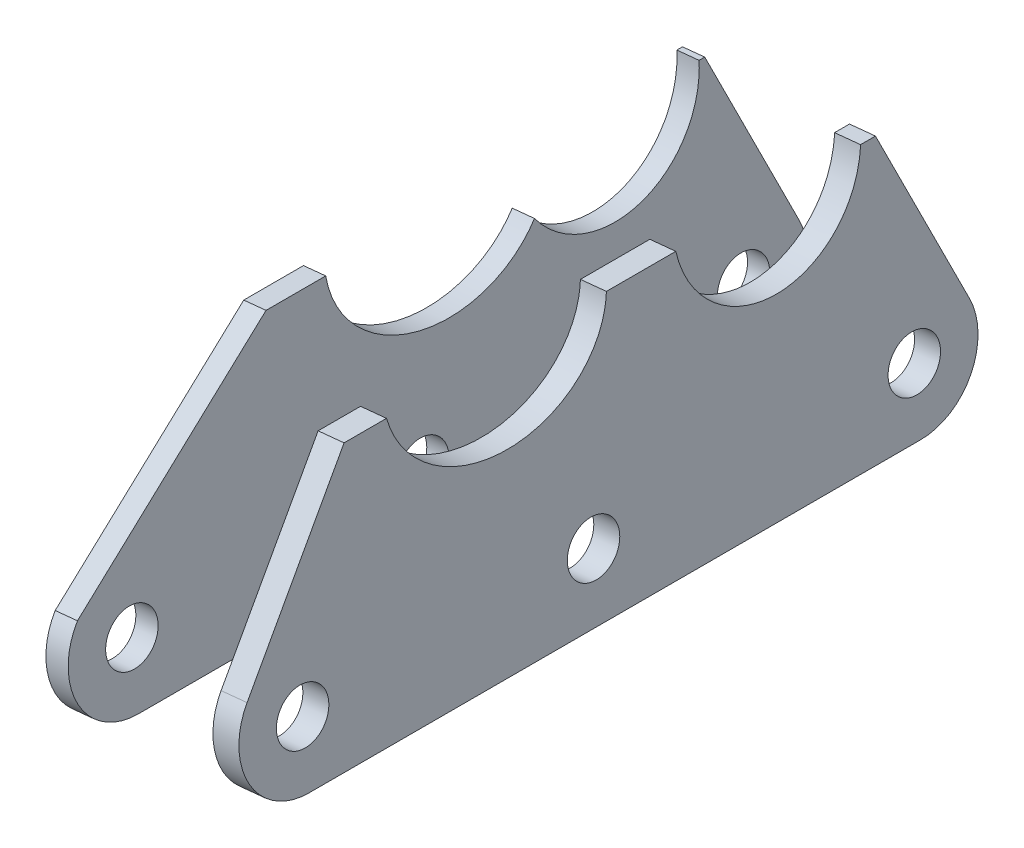
SolidWorks part; units mm, degrees
material "1.0545 (S355N)"
ref_plane "Płaszczyzna XY" through (0, 0, 0) normal (0, 0, 1) x (1, 0, 0)
ref_plane "Płaszczyzna XZ" through (0, 0, 0) normal (0, 1, 0) x (1, 0, 0)
ref_plane "Płaszczyzna YZ" through (0, 0, 0) normal (1, 0, 0) x (0, 0, -1)
ref_plane "Płaszczyzna1" through (1510.2654, 150.1623, 0) normal (-0.9951, -0.0989, 0) x (0, 0, 1)
ref_plane "Płaszczyzna2" through (1487.3783, 147.8867, 0) normal (-0.9951, -0.0989, 0) x (0, 0, 1)
sketch "Szkic1" plane through (1510.2654, 150.1623, 0) normal (-0.9951, -0.0989, 0) x (0, 0, 1)
  line L0 (176, -389.2443) -> (94, -389.2443)
  line L1 (162.1321, -354.2443) -> (167.8211, -354.2443)
  line L2 (96.5848, -354.2443) -> (86.2462, -377.2616)
  line L3 (132.653, -354.2443) -> (123.3511, -354.2443)
  line L4 (96.5848, -354.2443) -> (98.5848, -354.2443)
  line L6 (123.3511, -354.2443) -> (132.653, -354.2443)
  line L7 (167.8211, -354.2443) -> (182.9628, -375.8689)
  circle A0 centre (176, -380.7443) radius 3.5
  circle A1 centre (137, -380.7443) radius 3.5
  circle A2 centre (94, -380.7443) radius 3.5
  arc A4 (86.2462, -377.2616) -> (94, -389.2443) centre (94, -380.7443) ccw
  arc A5 (176, -389.2443) -> (182.9628, -375.8689) centre (176, -380.7443) ccw
  circle A6 centre (94, -380.7443) radius 8.5 construction
  circle A7 centre (176, -380.7443) radius 8.5 construction
  spline S1 degree 3 poles (123.3511, -354.2443) (121.4518, -366.9917) (109.9538, -368.0776) (102.8081, -361.9435) (100.7003, -360.1342) (99.0558, -357.5281) (98.5848, -354.2443) knots 0.177742 0.177742 0.177742 0.177742 0.5 0.5 0.5 0.636368 0.636368 0.636368 0.636368 weights 0.54177 0.417579 0.570322 1 0.818175 0.685941 0.603297
  spline S3 degree 3 poles (162.1321, -354.2443) (157.8341, -374.6222) (135.0825, -371.9575) (132.653, -354.2443) knots 0.55574 0.55574 0.55574 0.55574 0.989987 0.989987 0.989987 0.989987 weights 0.801896 0.351992 0.404944 0.960751
  dimension "D1" = 7
  dimension "D2" = 7
  dimension "D4" = 35
  dimension "D5" = 125
  dimension "D6" = 2
  dimension "D3" = 5
extrude "Dodanie-wyciągnięcie1" add sketch "Szkic1" along normal blind 3.5
sketch "Szkic2" plane through (1487.3783, 147.8867, 0) normal (-0.9951, -0.0989, 0) x (0, 0, 1)
  line L0 (176, -389.2443) -> (94, -389.2443) construction
  line L1 (176, -389.2443) -> (94, -389.2443)
  line L2 (182.7922, -375.6339) -> (142.8522, -344.4501)
  line L3 (86.2462, -377.2616) -> (97.4075, -352.4127)
  line L4 (155.3965, -354.2443) -> (147.3923, -354.2443)
  line L5 (132.653, -354.2443) -> (123.3511, -354.2443) construction
  line L6 (96.5848, -354.2443) -> (97.3416, -354.2443)
  arc A1 (86.2462, -377.2616) -> (94, -389.2443) centre (94, -380.7443) ccw construction
  circle A2 centre (94, -380.7443) radius 3.5 construction
  circle A3 centre (137, -380.7443) radius 3.5 construction
  circle A4 centre (176, -380.7443) radius 3.5 construction
  arc A5 (176, -389.2443) -> (182.7922, -375.6339) centre (176, -380.7443) ccw
  arc A6 (86.2462, -377.2616) -> (94, -389.2443) centre (94, -380.7443) ccw
  circle A7 centre (94, -380.7443) radius 3.5
  circle A8 centre (137, -380.7443) radius 3.5
  circle A9 centre (176, -380.7443) radius 3.5
  spline S1 degree 3 poles (120.3281, -346.8705) (130.6371, -334.2702) (147.7047, -338.4756) (147.4282, -353.5478) (147.1516, -368.62) (129.9215, -373.2742) (120.07, -360.9377) knots 0 0 0 0 0.5 0.5 0.5 1 1 1 1 weights 1 0.529269 0.529269 1 0.529269 0.529269 1
  spline S3 degree 3 poles (118.0127, -344.2314) (136.9821, -360.5152) (120.6524, -379.538) (101.683, -363.2542) (82.7137, -346.9704) (99.0433, -327.9476) (118.0127, -344.2314) (136.9821, -360.5152) (120.6524, -379.538) knots -0.5 0 0 0 0.5 0.5 0.5 1 1 1 1.5 1.5 1.5 weights 1 0.333333 0.333333 1 0.333333 0.333333 1 0.333333 0.333333 only from (118.0127, -344.2314) to (118.0127, -344.2314)
extrude "Dodanie-wyciągnięcie2" add sketch "Szkic2" along normal blind 3 separate body contours S1 S3 L6 L3 A6 L1 A5 L2 L4 A9 A8 A7
